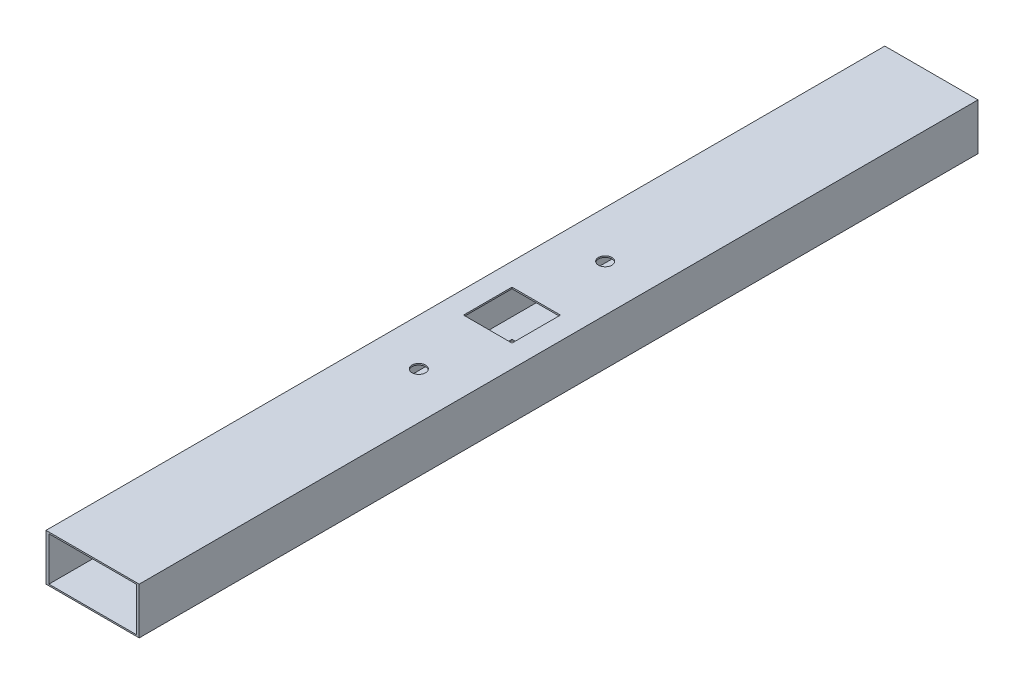
SolidWorks part; units mm, degrees
ref_plane "Front Plane" through (0, 0, 0) normal (0, 0, 1) x (1, 0, 0)
ref_plane "Top Plane" through (0, 0, 0) normal (0, 1, 0) x (1, 0, 0)
ref_plane "Right Plane" through (0, 0, 0) normal (1, 0, 0) x (0, 0, -1)
sketch "Sketch1" plane through (0, 0, 0) normal (0, 0, 1) x (1, 0, 0)
  line L1 (-25.4, 12.7) -> (25.4, 12.7)
  line L2 (-25.4, 12.7) -> (-25.4, -12.7)
  line L3 (-25.4, -12.7) -> (25.4, -12.7)
  line L4 (25.4, 12.7) -> (25.4, -12.7)
  line L5 (-25.4, 12.7) -> (25.4, -12.7) construction
  line L6 (-25.4, -12.7) -> (25.4, 12.7) construction
  line L7 (-23.8125, 11.9062) -> (23.8125, 11.9062)
  line L8 (-23.8125, 11.9062) -> (-23.8125, -11.9063)
  line L9 (-23.8125, -11.9063) -> (23.8125, -11.9063)
  line L10 (23.8125, 11.9062) -> (23.8125, -11.9063)
  line L11 (-23.8125, 11.9062) -> (23.8125, -11.9063) construction
  line L12 (-23.8125, -11.9063) -> (23.8125, 11.9062) construction
  point P0 (0, 0)
  point P6 (0, 0)
  dimension "D1" = 50.8
  dimension "D2" = 25.4
  dimension "D3" = 1.5875
extrude "Boss-Extrude1" add sketch "Sketch1" along normal blind 457.2
sketch "Sketch2" plane through (0, 12.7, 0) normal (0, 1, 0) x (1, 0, 0)
  line L0 (-25.4, -228.6) -> (25.4, -228.6) construction
  line L1 (-25.4, -457.2) -> (-25.4, 0) construction
  line L2 (25.4, -457.2) -> (25.4, 0) construction
  line L3 (0, -177.8) -> (0, -279.4) construction
  line L4 (-12.7, -215.9) -> (12.7, -215.9) construction
  line L5 (-12.7, -215.9) -> (-12.7, -241.3) construction
  line L6 (-12.7, -241.3) -> (12.7, -241.3) construction
  line L7 (12.7, -215.9) -> (12.7, -241.3) construction
  line L8 (-12.7, -215.9) -> (12.7, -241.3) construction
  line L9 (-12.7, -241.3) -> (12.7, -215.9) construction
  line L10 (-13.208, -215.392) -> (13.208, -215.392)
  line L11 (-13.208, -215.392) -> (-13.208, -241.808)
  line L12 (-13.208, -241.808) -> (13.208, -241.808)
  line L13 (13.208, -215.392) -> (13.208, -241.808)
  line L14 (-13.208, -215.392) -> (13.208, -241.808) construction
  line L15 (-13.208, -241.808) -> (13.208, -215.392) construction
  circle A0 centre (0, -177.8) radius 3.175 construction
  circle A1 centre (0, -177.8) radius 3.683
  circle A2 centre (0, -279.4) radius 3.683
  point P6 (0, -228.6)
  point P11 (0, -228.6)
  point P19 (0, -228.6)
  dimension "D6" = 6.35
  dimension "D7" = 0.508
  dimension "D1" = 25.4
  dimension "D2" = 25.4
  dimension "D3" = 0.508
  dimension "D4" = 0.508
  dimension "D5" = 101.6
extrude "Cut-Extrude1" cut sketch "Sketch2" against normal through all
